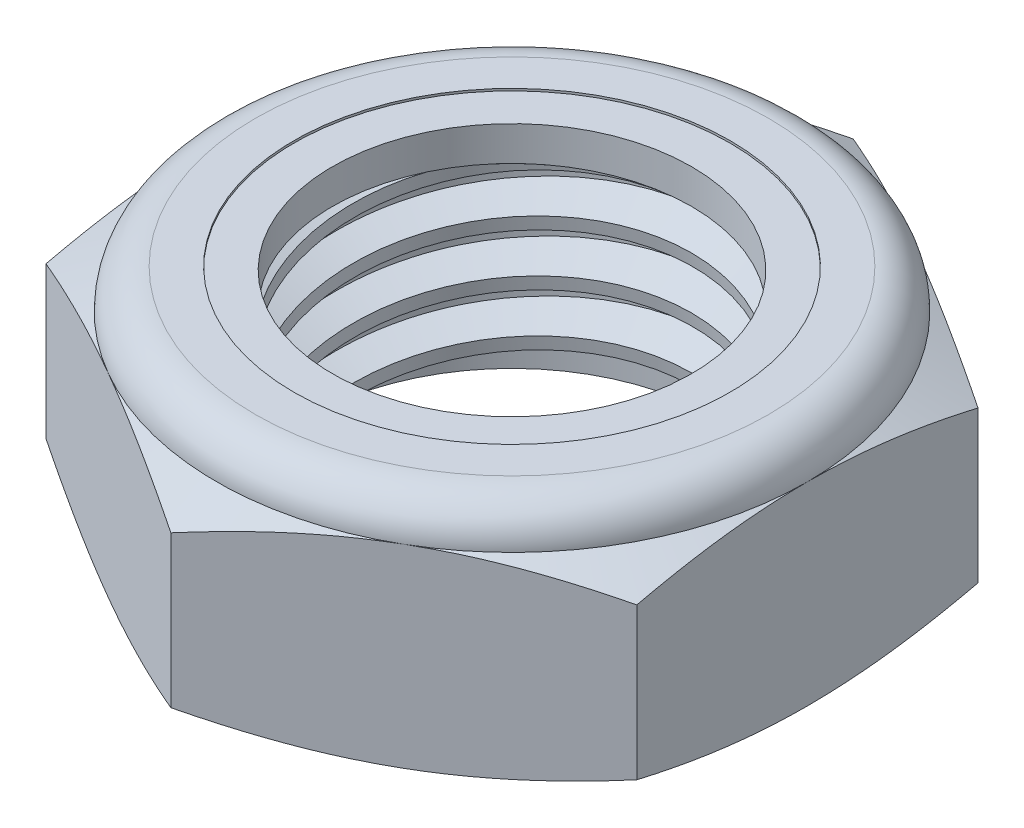
SolidWorks part; units mm, degrees
material "Plain Carbon Steel"
ref_plane "Front" through (0, 0, 0) normal (0, 0, 1) x (1, 0, 0)
ref_plane "Top" through (0, 0, 0) normal (0, 1, 0) x (1, 0, 0)
ref_plane "Right" through (0, 0, 0) normal (1, 0, 0) x (0, 0, -1)
sketch "Sketch1" plane through (0, 0, 0) normal (0, 1, 0) x (1, 0, 0)
  line L1 (0, 23.8301) -> (-20.6375, 11.9151)
  line L2 (-20.6375, 11.9151) -> (-20.6375, -11.9151)
  line L3 (-20.6375, -11.9151) -> (0, -23.8301)
  line L4 (0, -23.8301) -> (20.6375, -11.9151)
  line L5 (20.6375, -11.9151) -> (20.6375, 11.9151)
  line L6 (20.6375, 11.9151) -> (0, 23.8301)
  circle A0 centre (0, 0) radius 20.6375 construction
  dimension "Hex Flats" = 41.275
extrude "Extrude1" add sketch "Sketch1" along normal blind 16.2719
sketch "Sketch2" plane through (0, 0, 0) normal (1, 0, 0) x (0, 0, -1)
  line L0 (-14.2875, 0) -> (-14.2875, 16.2719) construction
  line L1 (0, 0) -> (14.2875, 0)
  line L2 (0, 0) -> (0, 16.2719)
  line L3 (0, 16.2719) -> (14.2875, 16.2719)
  line L4 (14.2875, 0) -> (14.2875, 16.2719)
  line L5 (-11.9151, 16.2719) -> (11.9151, 16.2719) construction
  line L7 (0, -14.2875) -> (0, 0) construction
  dimension "Thread Dia" = 28.575
revolve "Revolve1" add sketch "Sketch2" angle 360 about L7
sketch "Sketch3" plane through (0, 0, 0) normal (1, 0, 0) x (0, 0, -1)
  line L0 (14.2875, 16.2719) -> (-14.2875, 16.2719) construction
  line L1 (-14.2875, 16.2719) -> (-14.2875, 12.6433) construction
  line L2 (-14.2875, 12.6433) -> (14.2875, 16.2719) construction
  line L3 (14.2875, 16.2719) -> (14.3446, 15.8219) construction
  line L4 (14.3446, 15.8219) -> (14.7446, 12.6722)
  line L5 (14.7446, 12.6722) -> (12.6534, 13.5497)
  line L6 (12.6534, 13.5497) -> (12.5391, 14.4496)
  line L7 (12.5391, 14.4496) -> (14.3446, 15.8219)
  line L8 (12.5962, 13.9997) -> (14.5446, 14.2471) construction
  line L9 (14.2875, 16.2719) -> (14.2875, 14.2144) construction
  line L10 (14.2875, 14.2144) -> (-14.2875, 10.5858) construction
  line L11 (-14.2875, 10.5858) -> (-14.2875, 12.6433) construction
  line L12 (-0.4917, 16.2719) -> (0.4917, 8.5284) construction
  line L13 (-14.2875, 0) -> (-14.2875, 16.2719) construction
  line L14 (0, 16.2719) -> (14.2875, 16.2719) construction
  line L15 (14.2875, 0) -> (14.2875, 16.2719) construction
  point P13 (0, 12.4001)
  dimension "D1" = 0.4536
  dimension "D2" = 0.9071
  dimension "Thread Pitch" = 3.6286
  dimension "D4" = 60
  dimension "D5" = 3.6286
revolve "Cut-Revolve1" cut sketch "Sketch3" angle 360 about L12
pattern_linear "LPattern1" count 4 spacing 3.6286 along (0, -1, 0) count 2 spacing 3.6286 along (0, 1, 0) of "Cut-Revolve1"
sketch "Sketch4" plane through (0, 0, 0) normal (1, 0, 0) x (0, 0, -1)
  line L0 (0, 16.2719) -> (14.2875, 16.2719)
  line L1 (14.2875, 16.2719) -> (12.5391, 15.4566)
  line L2 (12.5391, 15.4566) -> (12.5391, 0.8153)
  line L3 (12.5391, 0.8153) -> (14.2875, 0)
  line L4 (14.2875, 0) -> (0, 0)
  line L5 (0, 0) -> (0, 16.2719)
  line L6 (14.2875, 0) -> (14.2875, 16.2719) construction
  line L7 (0, 16.2719) -> (14.2875, 16.2719) construction
  line L8 (0, 0) -> (14.2875, 0) construction
  line L9 (0, 0) -> (0, 16.2719) construction
  line L10 (0, 16.2719) -> (0, 18.201) construction
  dimension "D1" = 25
revolve "Cut-Revolve2" cut sketch "Sketch4" angle 360 about L10
combine bodies "Combine1" operation type subtract main body 112 bodies to subtract 111
sketch "Sketch5" plane through (0, 0, 0) normal (1, 0, 0) x (0, 0, -1)
  line L0 (0, 0) -> (20.6375, 0)
  line L1 (20.6375, 0) -> (23.8301, 1.4887)
  line L2 (23.8301, 1.4887) -> (23.8301, 12.0711)
  line L3 (23.8301, 12.0711) -> (20.6375, 13.5599)
  line L4 (17.9255, 16.2719) -> (17.9255, 17.5419)
  line L5 (17.9255, 17.5419) -> (25.1001, 17.5419)
  line L6 (25.1001, 17.5419) -> (25.1001, -1.27)
  line L7 (25.1001, -1.27) -> (0, -1.27)
  line L8 (0, -1.27) -> (0, 0)
  line L9 (20.6375, 13.5599) -> (20.6375, 0) construction
  line L10 (0, 0) -> (14.2875, 0) construction
  line L13 (23.8301, 6.7799) -> (25.1001, 6.7799) construction
  line L14 (23.8301, 16.2719) -> (23.8301, 0) construction
  line L15 (0, 0) -> (0, 17.5419) construction
  line L20 (0, 17.5419) -> (17.9255, 17.5419) construction
  line L22 (0, 16.2719) -> (14.2875, 16.2719) construction
  arc A0 (20.6375, 13.5599) -> (17.9255, 16.2719) centre (17.9255, 13.5599) ccw
  dimension "D1" = 25
  dimension "D2" = 1.27
  dimension "D3" = 16.2719
  dimension "D4" = 2.712
revolve "Cut-Revolve3" cut sketch "Sketch5" angle 360 about L15
sketch "Sketch6" plane through (0, 0, 0) normal (1, 0, 0) x (0, 0, -1)
  line L0 (0, 13.5599) -> (20.4851, 13.5599)
  line L1 (17.9255, 16.1195) -> (15.2323, 16.1195)
  line L2 (0, 17.5419) -> (0, 13.5599)
  line L3 (15.2323, 17.5419) -> (0, 17.5419)
  line L4 (0, 17.5419) -> (17.9255, 17.5419) construction
  line L5 (0, 0) -> (0, 17.5419) construction
  line L6 (0, 17.5419) -> (0, 44.323) construction
  line L7 (15.2323, 16.1195) -> (15.2323, 17.5419)
  line L8 (17.9255, 16.2719) -> (17.9255, 16.1195) construction
  line L9 (15.2323, 16.1195) -> (12.5391, 16.1195) construction
  line L10 (12.5391, 16.1195) -> (12.5391, 15.4566) construction
  arc A0 (20.4851, 13.5599) -> (17.9255, 16.1195) centre (17.9255, 13.5599) ccw
  arc A1 (20.6375, 13.5599) -> (17.9255, 16.2719) centre (17.9255, 13.5599) ccw construction
  dimension "D1" = 0.1524
revolve "Cut-Revolve4" cut sketch "Sketch6" angle 360 about L6
sketch "Sketch7" plane through (0, 0, 0) normal (1, 0, 0) x (0, 0, -1)
  line L0 (12.5391, 13.6361) -> (20.4077, 13.6361)
  line L1 (17.9255, 16.0433) -> (12.5391, 16.0433)
  line L2 (12.5391, 16.0433) -> (12.5391, 13.6361)
  line L3 (12.5391, 13.6361) -> (0, 13.6361) construction
  line L4 (0, 13.6361) -> (0, 16.0433) construction
  line L5 (0, 16.0433) -> (12.5391, 16.0433) construction
  line L6 (12.5391, 13.6361) -> (12.5391, 13.5599) construction
  line L7 (0, 13.5599) -> (20.4851, 13.5599) construction
  line L8 (17.9255, 16.0433) -> (17.9255, 16.1195) construction
  arc A0 (20.4077, 13.6361) -> (17.9255, 16.0433) centre (17.9255, 13.5599) ccw
  arc A2 (20.4851, 13.5599) -> (17.9255, 16.1195) centre (17.9255, 13.5599) ccw construction
  dimension "D1" = 0.0762
revolve "Revolve2" add sketch "Sketch7" angle 360 about L4
equation "\"D1@Sketch3\"=\"Thread Pitch@Sketch3\"/8"
equation "\"D2@Sketch3\"=\"Thread Pitch@Sketch3\"/4"
equation "\"D5@Sketch3\"=\"Thread Pitch@Sketch3\""
equation "\"D4@LPattern1\"=\"Thread Pitch@Sketch3\""
equation "\"D3@LPattern1\"=\"Thread Pitch@Sketch3\""
equation "\"D1@LPattern1\"=\"Height@Extrude1\"/\"Thread Pitch@Sketch3\""
equation "\"D4@Sketch5\"=\"Height@Extrude1\"/6"
